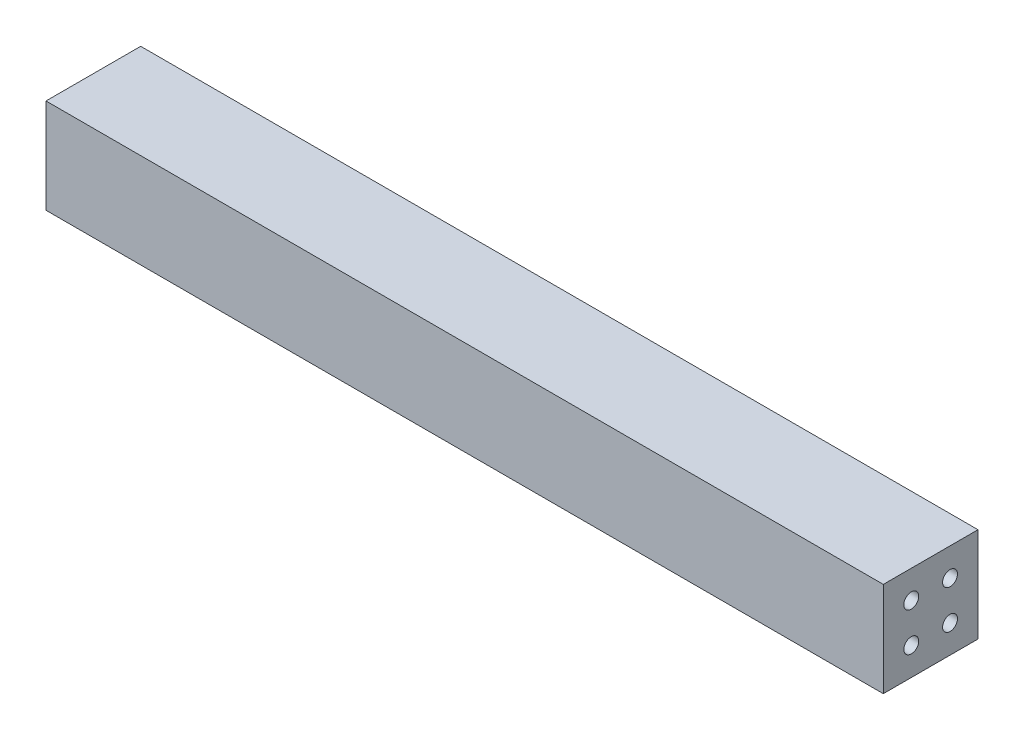
SolidWorks part; units mm, degrees
material "Pino"
ref_plane "Alzado" through (0, 0, 0) normal (0, 0, 1) x (1, 0, 0)
ref_plane "Planta" through (0, 0, 0) normal (0, 1, 0) x (1, 0, 0)
ref_plane "Vista lateral" through (0, 0, 0) normal (1, 0, 0) x (0, 0, -1)
sketch "Croquis1" plane through (0, 0, 0) normal (0, 1, 0) x (1, 0, 0)
  line L1 (-224.6, 25.4) -> (224.6, 25.4)
  line L2 (-224.6, 25.4) -> (-224.6, -25.4)
  line L3 (-224.6, -25.4) -> (224.6, -25.4)
  line L4 (224.6, 25.4) -> (224.6, -25.4)
  line L5 (-224.6, 25.4) -> (224.6, -25.4) construction
  line L6 (-224.6, -25.4) -> (224.6, 25.4) construction
  point P0 (0, 0)
  dimension "D1" = 50.8
  dimension "D2" = 449.2
extrude "Saliente-Extruir1" add sketch "Croquis1" along normal blind 50.8
sketch "Croquis2" plane through (224.6, 0, 0) normal (1, 0, 0) x (0, 0, -1)
  line L0 (-25.4, 0) -> (25.4, 0) construction
  line L1 (-25.4, 50.8) -> (-25.4, 0) construction
  line L2 (-25.4, 50.8) -> (25.4, 50.8) construction
  line L3 (-25.4, 50.8) -> (25.4, 0) construction
  line L4 (25.4, 50.8) -> (-25.4, 0) construction
  line L5 (25.4, 50.8) -> (-25.4, 0) construction
  line L6 (25.4, 0) -> (-25.4, 50.8) construction
  line L7 (-25.4, 0) -> (25.4, 50.8) construction
  circle A0 centre (-10.4, 35.8) radius 4
  circle A1 centre (10.4, 35.8) radius 4
  circle A2 centre (10.4, 15) radius 4
  circle A3 centre (-10.4, 15) radius 4
  point P29 (0, 25.4)
  dimension "D1" = 8
  dimension "D2" = 15
  dimension "D3" = 15
  dimension "D5" = 15
  dimension "D4" = 4
extrude "Cortar-Extruir1" cut sketch "Croquis2" against normal blind 10
sketch "Croquis3" plane through (-224.6, 0, 0) normal (-1, 0, 0) x (0, 0, 1)
  circle A0 centre (10.4, 35.8) radius 4
  circle A1 centre (10.4, 35.8) radius 4 construction
  circle A2 centre (10.4, 35.8) radius 4 construction
  circle A3 centre (-10.4, 35.8) radius 4
  circle A4 centre (-10.4, 15) radius 4
  circle A5 centre (10.4, 15) radius 4
  circle A6 centre (-10.4, 35.8) radius 4 construction
  circle A7 centre (10.4, 15) radius 4 construction
  circle A9 centre (-10.4, 15) radius 4 construction
extrude "Cortar-Extruir2" cut sketch "Croquis3" against normal blind 10
